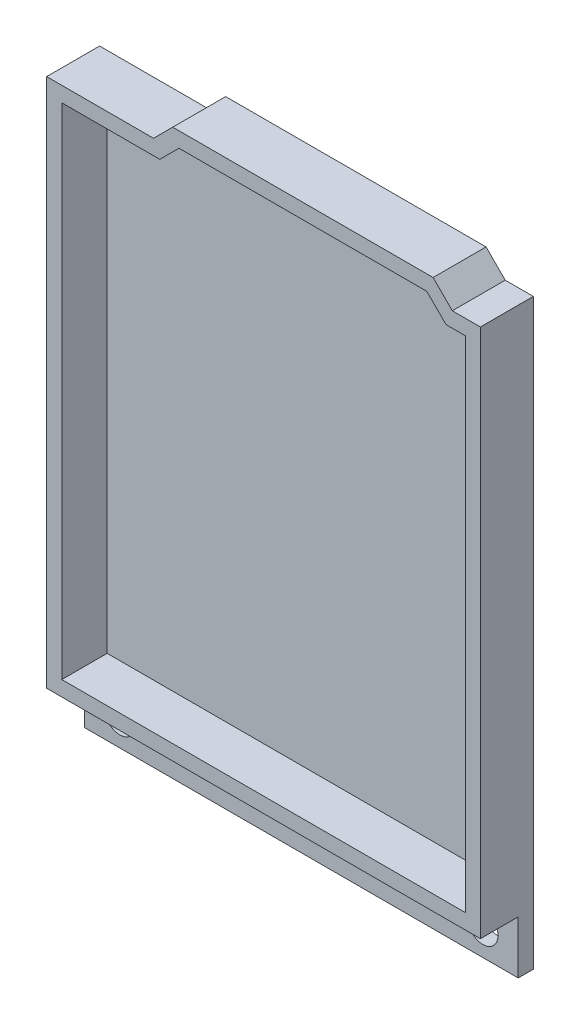
SolidWorks part; units mm, degrees
ref_plane "Front Plane" through (0, 0, 0) normal (0, 0, 1) x (1, 0, 0)
ref_plane "Top Plane" through (0, 0, 0) normal (0, 1, 0) x (1, 0, 0)
ref_plane "Right Plane" through (0, 0, 0) normal (1, 0, 0) x (0, 0, -1)
sketch "Sketch1" plane through (0, 0, 0) normal (0, 0, 1) x (1, 0, 0)
  line L0 (-53.34, 0) -> (-53.34, 66.04) construction
  line L1 (0, 0) -> (-53.34, 0) construction
  line L2 (0, 66.04) -> (0, 0) construction
  line L3 (-2.54, 66.04) -> (0, 66.04) construction
  line L4 (-5.08, 68.58) -> (-2.54, 66.04) construction
  line L5 (-37.846, 68.58) -> (-5.08, 68.58) construction
  line L6 (-40.386, 66.04) -> (-37.846, 68.58) construction
  line L7 (-53.34, 66.04) -> (-40.386, 66.04) construction
  line L8 (-53.34, 0) -> (-53.34, 66.04)
  line L9 (0, 0) -> (-53.34, 0)
  line L10 (0, 66.04) -> (0, 0)
  line L11 (-2.54, 66.04) -> (0, 66.04)
  line L12 (-5.08, 68.58) -> (-2.54, 66.04)
  line L13 (-37.846, 68.58) -> (-5.08, 68.58)
  line L14 (-40.386, 66.04) -> (-37.846, 68.58)
  line L15 (-53.34, 66.04) -> (-40.386, 66.04)
  line L16 (2, -2) -> (-55.34, -2)
  line L17 (-55.34, -2) -> (-55.34, 68.04)
  line L18 (-55.34, 68.04) -> (-41.2144, 68.04)
  line L19 (-41.2144, 68.04) -> (-38.6744, 70.58)
  line L20 (-38.6744, 70.58) -> (-4.2516, 70.58)
  line L21 (-4.2516, 70.58) -> (-1.7116, 68.04)
  line L22 (-1.7116, 68.04) -> (2, 68.04)
  line L23 (2, 68.04) -> (2, -2)
  dimension "D1" = 2
extrude "Boss-Extrude1" add sketch "Sketch1" against normal blind 7
sketch "Sketch2" plane through (0, 0, -7) normal (0, 0, -1) x (-1, 0, 0)
  line L0 (53.34, 0) -> (0, 0) construction
  line L1 (53.34, 66.04) -> (53.34, 0) construction
  line L2 (40.386, 66.04) -> (53.34, 66.04) construction
  line L3 (37.846, 68.58) -> (40.386, 66.04) construction
  line L4 (5.08, 68.58) -> (37.846, 68.58) construction
  line L5 (2.54, 66.04) -> (5.08, 68.58) construction
  line L6 (0, 66.04) -> (2.54, 66.04) construction
  line L7 (0, 0) -> (0, 66.04) construction
  line L8 (53.34, 0) -> (0, 0)
  line L9 (53.34, 66.04) -> (53.34, 0)
  line L10 (40.386, 66.04) -> (53.34, 66.04)
  line L11 (37.846, 68.58) -> (40.386, 66.04)
  line L12 (5.08, 68.58) -> (37.846, 68.58)
  line L13 (2.54, 66.04) -> (5.08, 68.58)
  line L14 (0, 66.04) -> (2.54, 66.04)
  line L15 (0, 0) -> (0, 66.04)
extrude "Boss-Extrude2" add sketch "Sketch2" against normal blind 1
sketch "Sketch3" plane through (0, 0, -7) normal (0, 0, -1) x (-1, 0, 0)
  line L0 (-2, -2) -> (-2, 68.04) construction
  line L1 (55.34, -2) -> (-2, -2)
  line L2 (55.34, -2) -> (55.34, -9)
  line L3 (55.34, -9) -> (-2, -9)
  line L4 (-2, -2) -> (-2, -9)
  dimension "D1" = 7
extrude "Boss-Extrude3" add sketch "Sketch3" against normal blind 2
sketch "Sketch4" plane through (0, 0, -5) normal (0, 0, 1) x (1, 0, 0)
  line L0 (2, -9) -> (-55.34, -9) construction
  line L1 (-26.67, -2) -> (-26.67, -9) construction
  line L2 (-55.34, -2) -> (2, -2) construction
  circle A0 centre (-2.67, -5.5) radius 2
  circle A1 centre (-50.67, -5.5) radius 2
  dimension "D1" = 4
  dimension "D2" = 4
  dimension "D3" = 48
  dimension "D4" = 3.5
  dimension "D5" = 24
extrude "Cut-Extrude1" cut sketch "Sketch4" against normal blind 2
